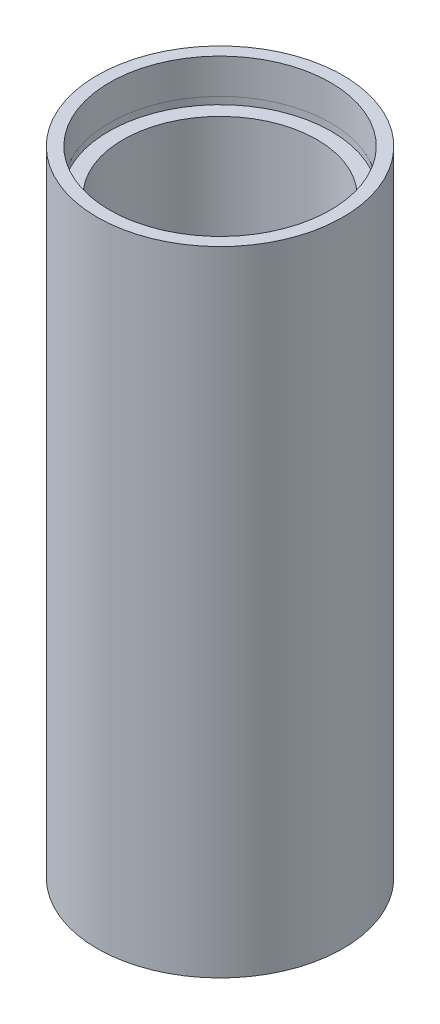
SolidWorks part; units mm, degrees
ref_plane "前视基准面" through (0, 0, 0) normal (0, 0, 1) x (1, 0, 0)
ref_plane "上视基准面" through (0, 0, 0) normal (0, 1, 0) x (1, 0, 0)
ref_plane "右视基准面" through (0, 0, 0) normal (1, 0, 0) x (0, 0, -1)
sketch "草图1" plane through (0, 0, 0) normal (0, 0, 1) x (1, 0, 0)
  line L0 (0, 161.3762) -> (0, 0) construction
  line L1 (141.7365, 0) -> (-131.7984, 0) construction
  line L2 (13.75, 0) -> (13.75, 4.5)
  line L3 (15.85, 0) -> (15.85, 81.7)
  line L4 (14.35, 4.5) -> (14.35, 5.5)
  line L5 (13.75, 4.5) -> (14.35, 4.5)
  line L6 (12.5, 5.5) -> (12.5, 76.2)
  line L7 (12.5, 5.5) -> (14.35, 5.5)
  line L8 (14.25, 81.7) -> (14.25, 77.2)
  line L9 (15.85, 81.7) -> (14.25, 81.7)
  line L10 (14.35, 77.2) -> (14.35, 76.2)
  line L11 (14.25, 77.2) -> (14.35, 77.2)
  line L12 (12.5, 76.2) -> (14.35, 76.2)
  line L13 (13.75, 0) -> (15.85, 0)
  dimension "D1" = 13.75
  dimension "D2" = 15.85
  dimension "D3" = 14.35
  dimension "D4" = 12.5
  dimension "D5" = 4.5
  dimension "D6" = 1
  dimension "D7" = 76.2
  dimension "D8" = 14.25
  dimension "D9" = 14.35
  dimension "D10" = 1
  dimension "D11" = 4.5
revolve "旋转1" add sketch "草图1" angle 360 about L0
cosmetic thread "装饰螺纹线1" parameters "D2"=28.5
cosmetic thread "装饰螺纹线2" parameters "D2"=26
cosmetic thread "装饰螺纹线3" parameters "D2"=28.51
